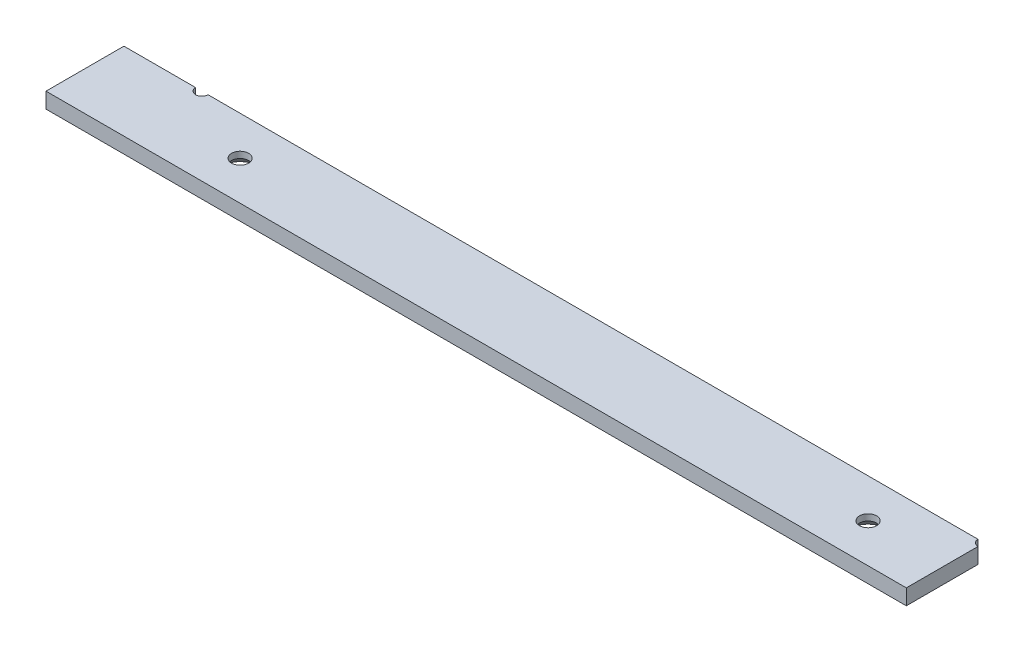
SolidWorks part; units mm, degrees
material "Acrílico (Impacto medio-alto)"
ref_plane "Alzado" through (0, 0, 0) normal (0, 0, 1) x (1, 0, 0)
ref_plane "Planta" through (0, 0, 0) normal (0, 1, 0) x (1, 0, 0)
ref_plane "Vista lateral" through (0, 0, 0) normal (1, 0, 0) x (0, 0, -1)
sketch "Croquis1" plane through (0, 0, 0) normal (0, 1, 0) x (1, 0, 0)
  line L1 (0, 0) -> (276, 0)
  line L2 (0, 0) -> (0, 25)
  line L3 (0, 25) -> (276, 25)
  line L4 (276, 0) -> (276, 25)
  dimension "D1" = 25
  dimension "D2" = 276
extrude "Saliente-Extruir1" add sketch "Croquis1" along normal blind 5
sketch "Croquis2" plane through (0, 5, 0) normal (0, 1, 0) x (1, 0, 0)
  line L0 (25, 25) -> (25, 0) construction
  line L1 (276, 25) -> (0, 25) construction
  line L2 (0, 0) -> (276, 0) construction
  line L3 (0, 25) -> (0, 0) construction
  circle A0 centre (276, 25) radius 2
  circle A1 centre (25, 25) radius 2
  dimension "D1" = 4
  dimension "D3" = 4
  dimension "D2" = 25
extrude "Cortar-Extruir1" cut sketch "Croquis2" against normal blind 5
sketch "Croquis3" plane through (0, 0, 0) normal (0, -1, 0) x (1, 0, 0)
  line L0 (150.5, -25) -> (150.5, 0) construction
  line L1 (274, -25) -> (27, -25) construction
  line L2 (0, 0) -> (276, 0) construction
  line L3 (0, -25) -> (0, 0) construction
  circle A0 centre (49.7688, -12.5) radius 2
  circle A1 centre (251.2312, -12.5) radius 2
  dimension "D2" = 4
  dimension "D1" = 150.5
hole_wizard "Avellanado para tornillo con cabeza avellanada de clavija hexagonal de M51" positions "Croquis5" profile "Croquis4" countersink size "M5" standard "DIN"
sketch "Croquis5" plane through (0, 0, 0) normal (0, -1, 0) x (-1, 0, 0)
  point P0 (-251.2312, 12.5)
  point P3 (-49.7688, 12.5)
sketch "Croquis4" plane through (251.2312, 0, -12.5) normal (1, 0, 0) x (0, 0, -1)
  line L0 (0, 0) -> (0, 6.6524)
  line L1 (0, 6.6524) -> (2.75, 5)
  line L2 (2.75, 5) -> (2.75, 2.985)
  line L3 (2.75, 2.985) -> (5.735, 0)
  line L5 (5.735, 0) -> (0, 0)
  line L6 (-2.75, 2.985) -> (-5.735, 0) construction
  line L10 (0, 6.6524) -> (-2.75, 5) construction
  line L11 (0, -6.35) -> (0, 107.95) construction
  dimension "Diámetro de taladro" = 5.5
  dimension "Profundidad de taladro" = 5
  dimension "Ángulo de avellanado cercano" = 11.47
  dimension "Ángulo de avellanado lejano" = 90
  dimension "Ángulo de perforador" = 118
